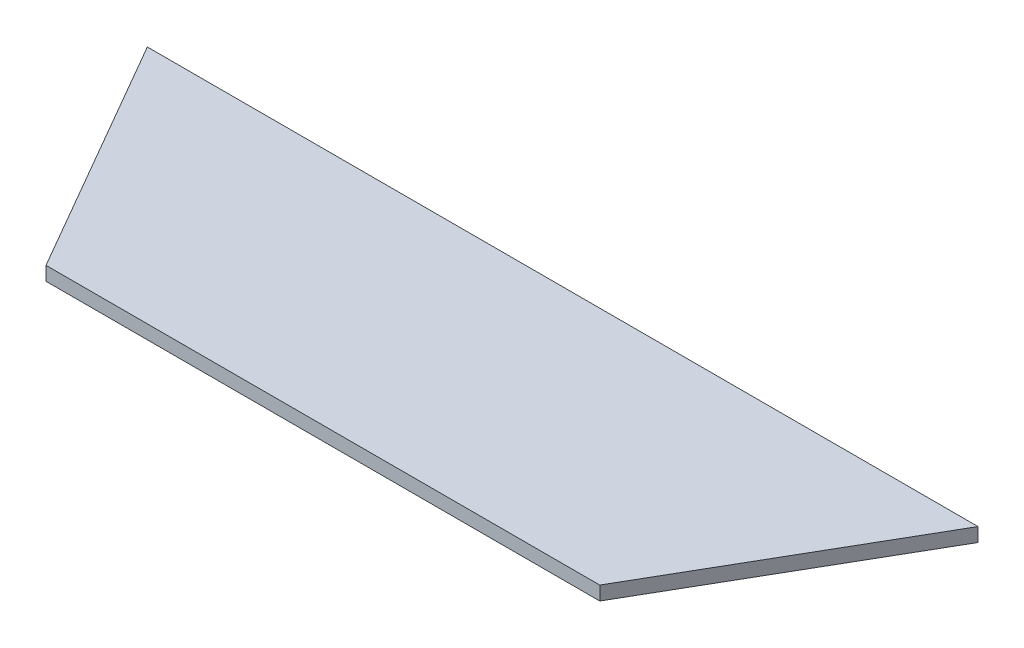
SolidWorks part; units mm, degrees
ref_plane "Front Plane" through (0, 0, 0) normal (0, 0, 1) x (1, 0, 0)
ref_plane "Top Plane" through (0, 0, 0) normal (0, 1, 0) x (1, 0, 0)
ref_plane "Right Plane" through (0, 0, 0) normal (1, 0, 0) x (0, 0, -1)
sketch "Sketch1" plane through (0, 0, 0) normal (0, 1, 0) x (1, 0, 0)
  line L0 (-150, -86.6025) -> (150, -86.6025) construction
  line L4 (-150, -86.6025) -> (-100, -173.2051)
  line L5 (-100, -173.2051) -> (100, -173.2051)
  line L6 (100, -173.2051) -> (150, -86.6025)
  line L7 (-150, -86.6025) -> (150, -86.6025)
  line L8 (200, 0) -> (100, 173.2051) [skipped]
  line L9 (-100, 173.2051) -> (-200, 0) [skipped]
  line L11 (100, 173.2051) -> (-100, 173.2051) [skipped]
  dimension "D1" = 200
extrude "Boss-Extrude1" add sketch "Sketch1" along normal blind 5
